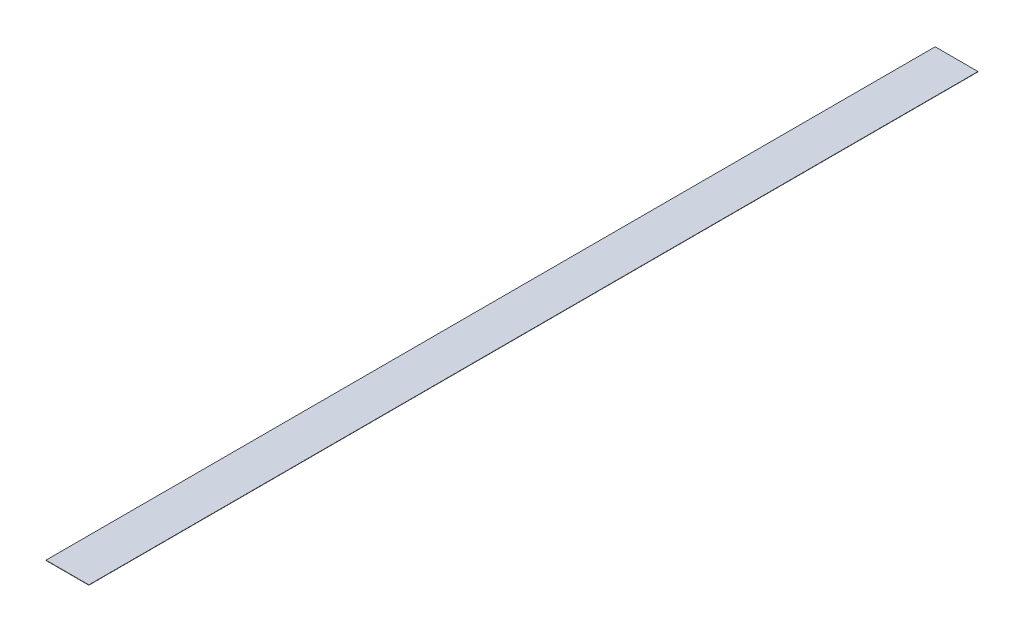
SolidWorks part; units mm, degrees
ref_plane "Front" through (0, 0, 0) normal (0, 0, 1) x (1, 0, 0)
ref_plane "Top" through (0, 0, 0) normal (0, 1, 0) x (1, 0, 0)
ref_plane "Right" through (0, 0, 0) normal (1, 0, 0) x (0, 0, -1)
sketch "Sketch1" plane through (0, 0, 0) normal (0, 1, 0) x (1, 0, 0)
  line L0 (-7.205, 149.5) -> (7.205, -149.5) construction
  line L1 (-7.205, 149.5) -> (7.205, 149.5)
  line L2 (-7.205, 149.5) -> (-7.205, -149.5)
  line L3 (-7.205, -149.5) -> (7.205, -149.5)
  line L4 (7.205, 149.5) -> (7.205, -149.5)
  point P4 (0, 0)
  dimension "D1" = 299
  dimension "D2" = 14.41
extrude "Extrude1" add sketch "Sketch1" along normal blind 0.1
